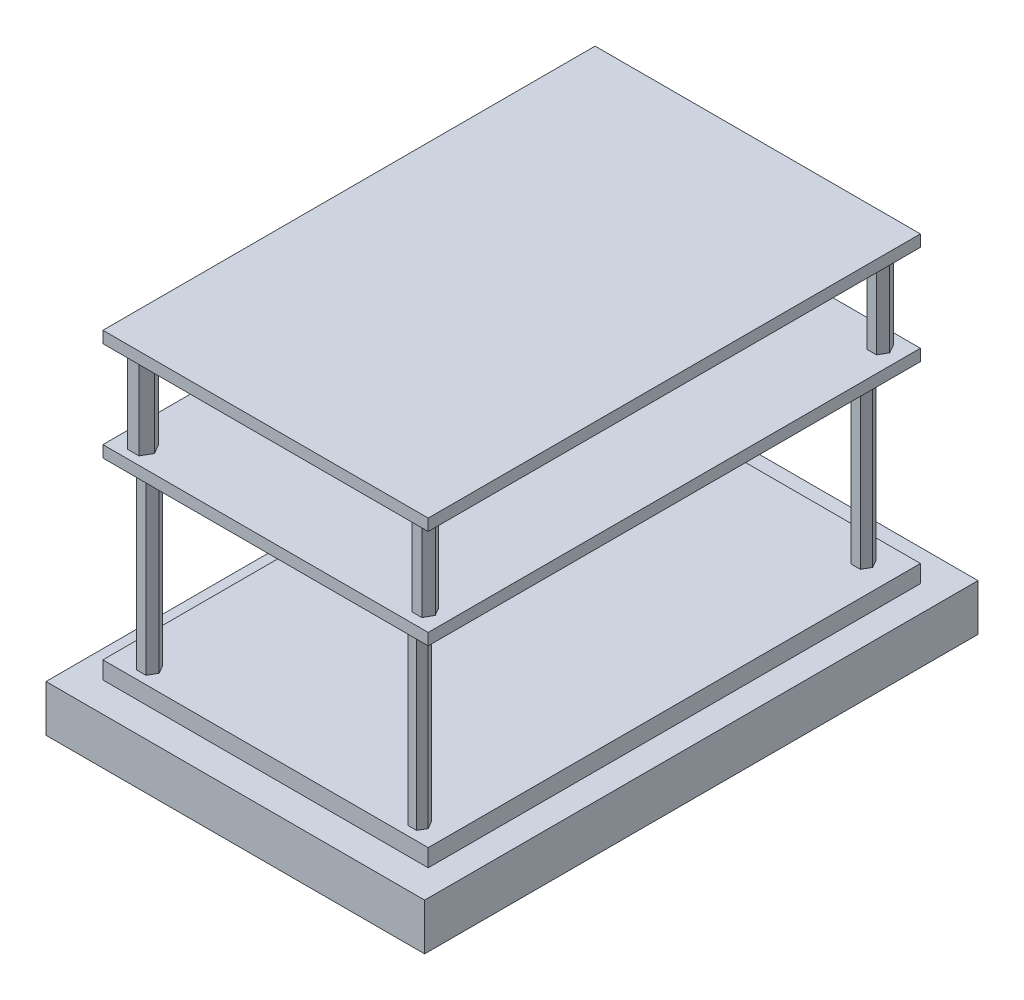
SolidWorks part; units mm, degrees
ref_plane "Front Plane" through (0, 0, 0) normal (0, 0, 1) x (1, 0, 0)
ref_plane "Top Plane" through (0, 0, 0) normal (0, 1, 0) x (1, 0, 0)
ref_plane "Right Plane" through (0, 0, 0) normal (1, 0, 0) x (0, 0, -1)
sketch "Sketch1" plane through (0, 0, 0) normal (0, 1, 0) x (1, 0, 0)
  line L1 (-80.0207, 51.639) -> (-15.0207, 51.639)
  line L2 (-80.0207, 51.639) -> (-80.0207, -43.361)
  line L3 (-80.0207, -43.361) -> (-15.0207, -43.361)
  line L4 (-15.0207, 51.639) -> (-15.0207, -43.361)
  dimension "D1" = 95
  dimension "D2" = 65
extrude "Boss-Extrude1" add sketch "Sketch1" along normal blind 8
sketch "Sketch2" plane through (0, 8, 0) normal (0, 1, 0) x (1, 0, 0)
  line L1 (-75.3556, 46.2405) -> (-19.5126, 46.2405)
  line L2 (-75.3556, 46.2405) -> (-75.3556, -38.2549)
  line L3 (-75.3556, -38.2549) -> (-19.5126, -38.2549)
  line L4 (-19.5126, 46.2405) -> (-19.5126, -38.2549)
extrude "Boss-Extrude2" add sketch "Sketch2" along normal blind 3
sketch "Sketch3" plane through (0, 11, 0) normal (0, 1, 0) x (1, 0, 0)
  line L1 (-68.5336, 41.5626) -> (-69.3619, 42.9974)
  line L2 (-69.3619, 42.9974) -> (-71.0187, 42.9974)
  line L3 (-71.0187, 42.9974) -> (-71.8471, 41.5626)
  line L4 (-71.8471, 41.5626) -> (-71.0187, 40.1278)
  line L5 (-71.0187, 40.1278) -> (-69.3619, 40.1278)
  line L6 (-69.3619, 40.1278) -> (-68.5336, 41.5626)
  line L7 (-23.021, 41.5626) -> (-23.8007, 42.913)
  line L8 (-23.8007, 42.913) -> (-25.36, 42.913)
  line L9 (-25.36, 42.913) -> (-26.1397, 41.5626)
  line L10 (-26.1397, 41.5626) -> (-25.36, 40.2122)
  line L11 (-25.36, 40.2122) -> (-23.8007, 40.2122)
  line L12 (-23.8007, 40.2122) -> (-23.021, 41.5626)
  line L13 (-22.3388, -35.4286) -> (-23.0698, -34.1626)
  line L14 (-23.0698, -34.1626) -> (-24.5316, -34.1626)
  line L15 (-24.5316, -34.1626) -> (-25.2626, -35.4286)
  line L16 (-25.2626, -35.4286) -> (-24.5316, -36.6946)
  line L17 (-24.5316, -36.6946) -> (-23.0698, -36.6946)
  line L18 (-23.0698, -36.6946) -> (-22.3388, -35.4286)
  line L19 (-68.5336, -35.4286) -> (-69.3619, -33.9938)
  line L20 (-69.3619, -33.9938) -> (-71.0187, -33.9938)
  line L21 (-71.0187, -33.9938) -> (-71.8471, -35.4286)
  line L22 (-71.8471, -35.4286) -> (-71.0187, -36.8634)
  line L23 (-71.0187, -36.8634) -> (-69.3619, -36.8634)
  line L24 (-69.3619, -36.8634) -> (-68.5336, -35.4286)
  circle A0 centre (-70.1903, 41.5626) radius 1.4348 construction
  circle A1 centre (-24.5804, 41.5626) radius 1.3504 construction
  circle A2 centre (-23.8007, -35.4286) radius 1.266 construction
  circle A3 centre (-70.1903, -35.4286) radius 1.4348 construction
extrude "Boss-Extrude3" add sketch "Sketch3" along normal blind 30
sketch "Sketch4" plane through (0, 41, 0) normal (0, 1, 0) x (1, 0, 0)
  line L1 (-75.3556, 46.2405) -> (-19.5126, 46.2405)
  line L2 (-75.3556, 46.2405) -> (-75.3556, -38.2549)
  line L3 (-75.3556, -38.2549) -> (-19.5126, -38.2549)
  line L4 (-19.5126, 46.2405) -> (-19.5126, -38.2549)
extrude "Boss-Extrude4" add sketch "Sketch4" along normal blind 2
sketch "Sketch5" plane through (0, 43, 0) normal (0, 1, 0) x (1, 0, 0)
  line L1 (-69.6056, 42.927) -> (-70.5802, 44.615)
  line L2 (-70.5802, 44.615) -> (-72.5293, 44.615)
  line L3 (-72.5293, 44.615) -> (-73.5039, 42.927)
  line L4 (-73.5039, 42.927) -> (-72.5293, 41.239)
  line L5 (-72.5293, 41.239) -> (-70.5802, 41.239)
  line L6 (-70.5802, 41.239) -> (-69.6056, 42.927)
  line L7 (-21.4617, 42.927) -> (-22.2901, 44.3618)
  line L8 (-22.2901, 44.3618) -> (-23.9469, 44.3618)
  line L9 (-23.9469, 44.3618) -> (-24.7753, 42.927)
  line L10 (-24.7753, 42.927) -> (-23.9469, 41.4922)
  line L11 (-23.9469, 41.4922) -> (-22.2901, 41.4922)
  line L12 (-22.2901, 41.4922) -> (-21.4617, 42.927)
  line L13 (-22.2901, -33.6669) -> (-23.9768, -33.6842)
  line L14 (-23.9768, -33.6842) -> (-24.8052, -35.1535)
  line L15 (-24.8052, -35.1535) -> (-23.9469, -36.6056)
  line L16 (-23.9469, -36.6056) -> (-22.2602, -36.5883)
  line L17 (-22.2602, -36.5883) -> (-21.4318, -35.119)
  line L18 (-21.4318, -35.119) -> (-22.2901, -33.6669)
  line L19 (-69.6056, -35.1535) -> (-70.5802, -33.4655)
  line L20 (-70.5802, -33.4655) -> (-72.5293, -33.4655)
  line L21 (-72.5293, -33.4655) -> (-73.5039, -35.1535)
  line L22 (-73.5039, -35.1535) -> (-72.5293, -36.8415)
  line L23 (-72.5293, -36.8415) -> (-70.5802, -36.8415)
  line L24 (-70.5802, -36.8415) -> (-69.6056, -35.1535)
  circle A0 centre (-71.5547, 42.927) radius 1.688 construction
  circle A1 centre (-23.1185, 42.927) radius 1.4348 construction
  circle A2 centre (-23.1185, -35.1362) radius 1.4608 construction
  circle A3 centre (-71.5547, -35.1535) radius 1.688 construction
extrude "Boss-Extrude5" add sketch "Sketch5" along normal blind 15
sketch "Sketch6" plane through (0, 58, 0) normal (0, 1, 0) x (1, 0, 0)
  line L1 (-75.3556, 46.2405) -> (-19.5126, 46.2405)
  line L2 (-75.3556, 46.2405) -> (-75.3556, -38.2549)
  line L3 (-75.3556, -38.2549) -> (-19.5126, -38.2549)
  line L4 (-19.5126, 46.2405) -> (-19.5126, -38.2549)
extrude "Boss-Extrude6" add sketch "Sketch6" along normal blind 2
